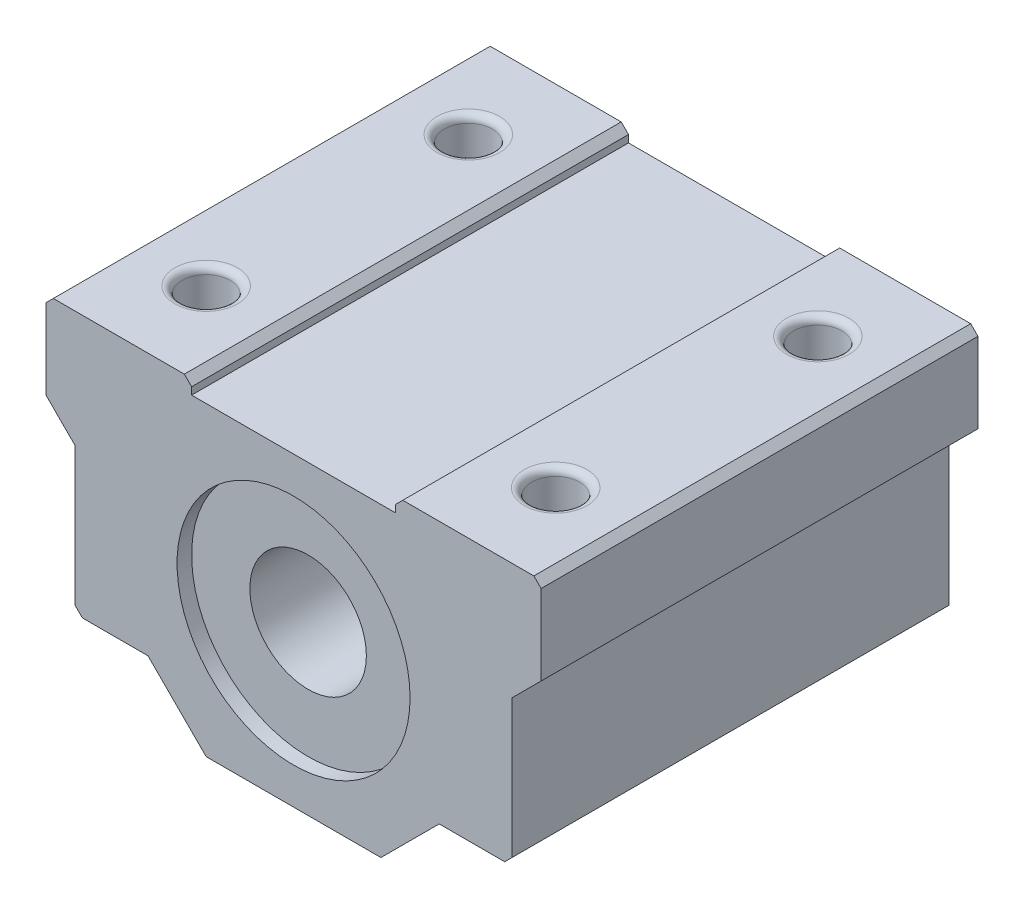
SolidWorks part; units mm, degrees
ref_plane "Front Plane" through (0, 0, 0) normal (0, 0, 1) x (1, 0, 0)
ref_plane "Top Plane" through (0, 0, 0) normal (0, 1, 0) x (1, 0, 0)
ref_plane "Right Plane" through (0, 0, 0) normal (1, 0, 0) x (0, 0, -1)
sketch "Sketch1" plane through (0, 0, 0) normal (0, 0, 1) x (1, 0, 0)
  line L0 (-17, 11.5) -> (-7, 11.5)
  line L1 (-6, -10.5) -> (6, -10.5)
  line L2 (6, -10.5) -> (10, -6.5)
  line L3 (10, -6.5) -> (15, -6.5)
  line L4 (15, -6.5) -> (15, 3.5)
  line L5 (15, 3.5) -> (17, 5.5)
  line L6 (17, 5.5) -> (17, 11.5)
  line L7 (0, -10.5) -> (0, 10.5) construction
  line L8 (-6, -10.5) -> (-10, -6.5)
  line L9 (-10, -6.5) -> (-15, -6.5)
  line L10 (-15, -6.5) -> (-15, 3.5)
  line L11 (-15, 3.5) -> (-17, 5.5)
  line L12 (-17, 5.5) -> (-17, 11.5)
  line L13 (-7, 10.5) -> (7, 10.5)
  line L14 (-7, 10.5) -> (-7, 11.5)
  line L15 (7, 10.5) -> (7, 11.5)
  line L16 (7, 11.5) -> (17, 11.5)
  circle A0 centre (0, 0) radius 8
  point P18 (0, 0)
  dimension "D13" = 16
  dimension "D1" = 22
  dimension "D2" = 18
  dimension "D3" = 6
  dimension "D4" = 6
  dimension "D5" = 18
  dimension "D6" = 1
  dimension "D7" = 12
  dimension "D8" = 20
  dimension "D9" = 14
  dimension "D10" = 30
  dimension "D11" = 2
  dimension "D12" = 34
extrude "Boss-Extrude1" add sketch "Sketch1" along normal mid plane 30
sketch "Sketch2" plane through (0, 11.5, 0) normal (0, 1, 0) x (1, 0, 0)
  line L0 (12, 0) -> (-12, 0) construction
  line L1 (-12, 0) -> (-12, 9) construction
  line L2 (0, 0) -> (0, -15) construction
  line L3 (7, -15) -> (-7, -15) construction
  line L4 (12, 0) -> (12, 9) construction
  circle A0 centre (-12, 9) radius 1.65
  circle A1 centre (-12, -9) radius 1.65
  circle A2 centre (12, -9) radius 1.65
  circle A3 centre (12, 9) radius 1.65
  dimension "D1" = 3.3
  dimension "D2" = 9
  dimension "D3" = 12
extrude "Cut-Extrude1" cut sketch "Sketch2" against normal through all
sketch "Sketch3" plane through (0, 0, 0) normal (0, 0, 1) x (1, 0, 0)
  circle A0 centre (0, 0) radius 4
  circle A1 centre (0, 0) radius 8
  circle A2 centre (0, 0) radius 8 construction
  dimension "D1" = 8
extrude "Boss-Extrude2" add sketch "Sketch3" along normal mid plane 28
fillet "Fillet1" radius 0.5 4 edges at (12, 11.5, -10.65) (12, 11.5, 10.65) (-12, 11.5, -7.35) (-12, 11.5, 7.35)
chamfer "Chamfer1" distance 0.5 angle 45 6 edges at (15, -6.5, 0) (-15, -6.5, 0) (-17, 11.5, 0) (-7, 11.5, 0) (7, 11.5, 0) (17, 11.5, 0)
